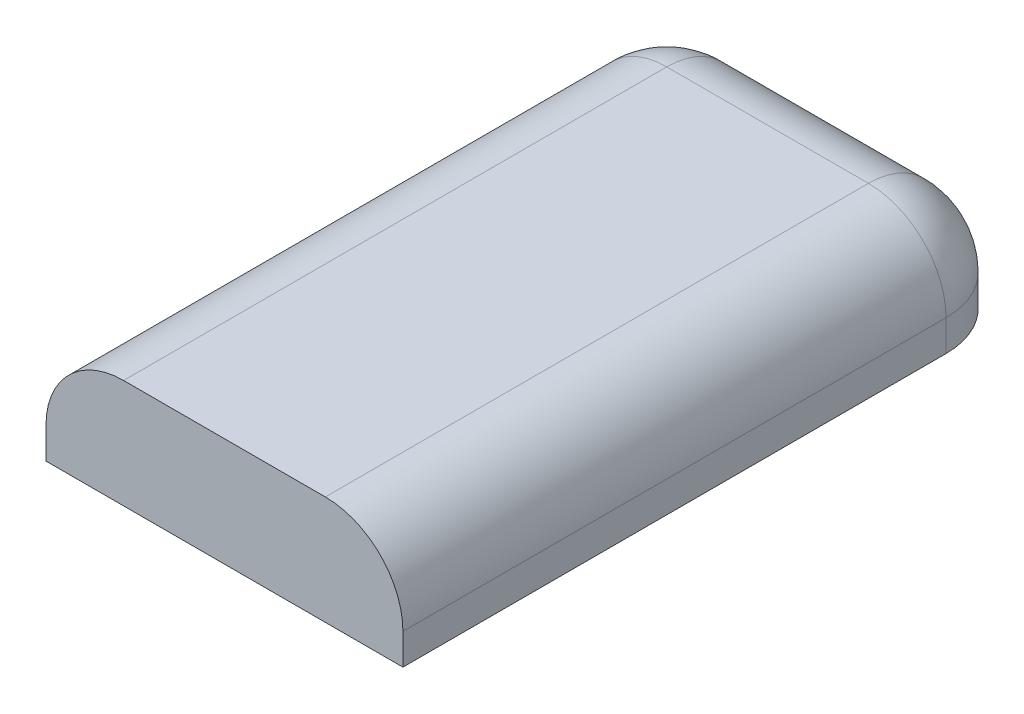
SolidWorks part; units mm, degrees
ref_plane "Front Plane" through (0, 0, 0) normal (0, 0, 1) x (1, 0, 0)
ref_plane "Top Plane" through (0, 0, 0) normal (0, 1, 0) x (1, 0, 0)
ref_plane "Right Plane" through (0, 0, 0) normal (1, 0, 0) x (0, 0, -1)
sketch "Sketch1" plane through (0, 0, 0) normal (0, 1, 0) x (1, 0, 0)
  line L1 (-11.5, 20) -> (11.5, 20)
  line L2 (-11.5, 20) -> (-11.5, -20)
  line L3 (-11.5, -20) -> (11.5, -20)
  line L4 (11.5, 20) -> (11.5, -20)
  line L5 (-11.5, 20) -> (11.5, -20) construction
  line L6 (-11.5, -20) -> (11.5, 20) construction
  point P0 (0, 0)
  dimension "D1" = 23
  dimension "D2" = 40
extrude "Boss-Extrude1" add sketch "Sketch1" along normal blind 7
fillet "Fillet1" radius 5 1 edges at (-11.5, 3.5, -20)
fillet "Fillet2" radius 5 1 edges at (11.5, 3.5, -20)
fillet "Fillet3" radius 5 5 edges at (-11.5, 7, 2.5) (-10.0355, 7, -18.5355) (0, 7, -20) (10.0355, 7, -18.5355) (11.5, 7, 2.5)
